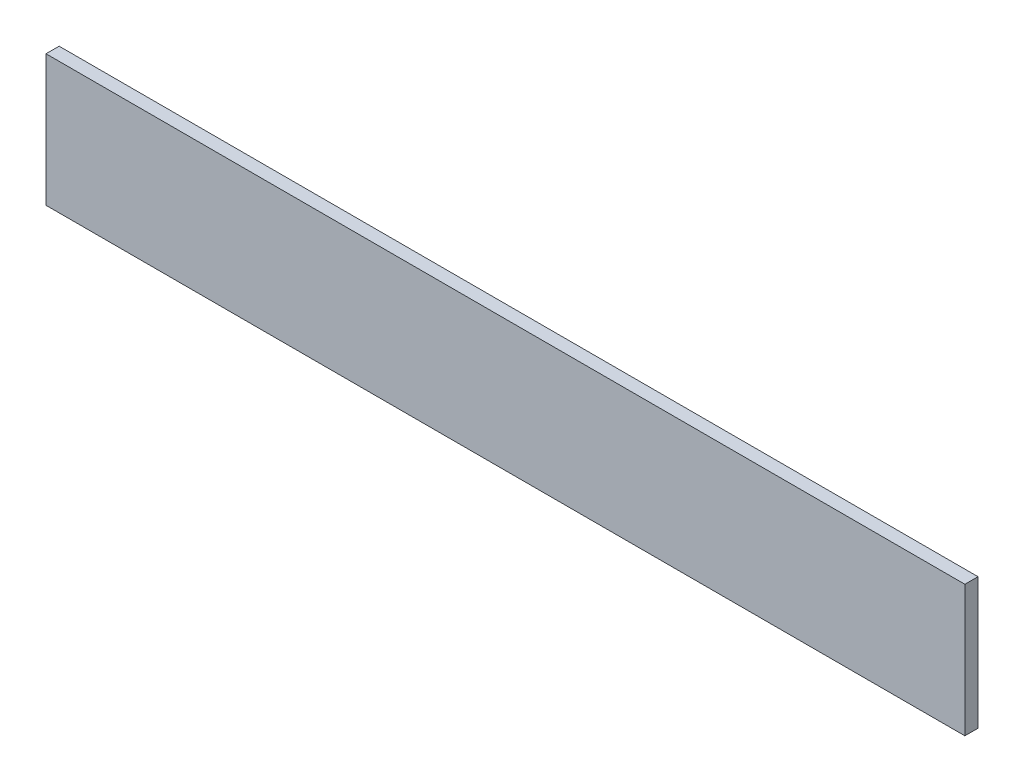
SolidWorks part; units mm, degrees
ref_plane "Спереди" through (0, 0, 0) normal (0, 0, 1) x (1, 0, 0)
ref_plane "Сверху" through (0, 0, 0) normal (0, 1, 0) x (1, 0, 0)
ref_plane "Справа" through (0, 0, 0) normal (1, 0, 0) x (0, 0, -1)
sketch "Эскиз1" plane through (0, 0, 0) normal (0, 0, 1) x (1, 0, 0)
  line L1 (0, 0) -> (140, 0)
  line L2 (0, 0) -> (0, -20)
  line L3 (0, -20) -> (140, -20)
  line L4 (140, 0) -> (140, -20)
extrude "Бобышка-Вытянуть1" add sketch "Эскиз1" along normal blind 2
